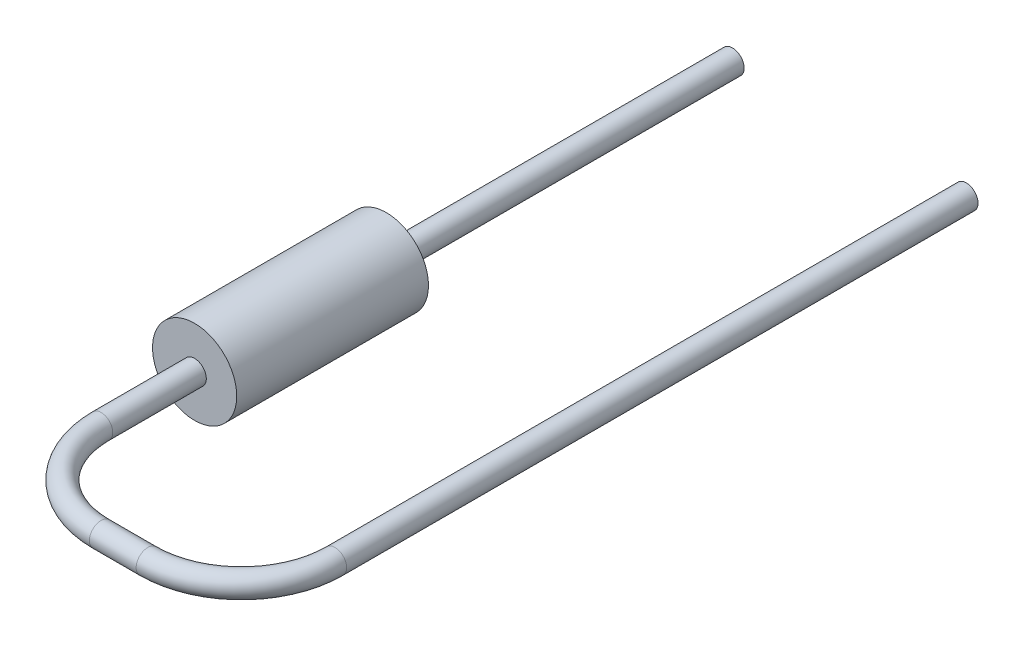
SolidWorks part; units mm, degrees
ref_plane "Top Plane" through (0, 0, 0) normal (0, 0, 1) x (1, 0, 0)
ref_plane "Front Plane" through (0, 0, 0) normal (0, 1, 0) x (1, 0, 0)
ref_plane "Right Plane" through (0, 0, 0) normal (1, 0, 0) x (0, 0, -1)
sketch "Sketch2" plane through (0, 0, 0) normal (0, 0, 1) x (1, 0, 0)
  circle A0 centre (0, 0) radius 0.9
  dimension "D1" = 1.8
extrude "Resistor Body" add sketch "Sketch2" along normal blind 4.1
sketch "Lead1 Path" plane through (0, 0, 0) normal (0, 1, 0) x (1, 0, 0)
  line L0 (5, -6.1) -> (5, 7.4)
  line L1 (-0.9, -4.1) -> (0.9, -4.1) construction
  line L2 (0, -4.1) -> (0, 0) construction
  line L3 (0, -4.1) -> (0, -6.1)
  line L5 (2, -8.1) -> (3, -8.1)
  arc A0 (2, -8.1) -> (0, -6.1) centre (2, -6.1) cw
  arc A1 (5, -6.1) -> (3, -8.1) centre (3, -6.1) cw
  point P9 (0, -8.1)
  point P11 (0, -8.1)
  dimension "D4" = 5
  dimension "D1" = 2
  dimension "D2" = 4
  dimension "D3" = 15.5
sketch "Lead1 Profile" plane through (0, 0, 4.1) normal (0, 0, 1) x (-1, 0, 0)
  circle A0 centre (0, 0) radius 0.25
  dimension "D1" = 0.5
sweep "Lead1" add profiles "Lead1 Profile" path "Lead1 Path"
sketch "Sketch6" plane through (0, 0, 0) normal (0, 0, 1) x (1, 0, 0)
  circle A0 centre (0, 0) radius 0.25 construction
  circle A1 centre (0, 0) radius 0.25
extrude "Lead2" add sketch "Sketch6" along normal up to surface (7.4 mm away)
ref_plane "Mounting Plane" through (0, 0, -4) normal (0, 0, 1) x (1, 0, 0)
sketch "Component_Outline" plane through (0, 0, -4) normal (0, 0, 1) x (1, 0, 0)
  line L0 (0.8646, 0.25) -> (5, 0.25)
  line L1 (2, 0.25) -> (0, 0.25) construction
  line L2 (5, -0.25) -> (0.8646, -0.25)
  line L3 (0, -0.25) -> (2, -0.25) construction
  arc A0 (0.8646, 0.25) -> (0.8646, -0.25) centre (0, 0) ccw
  arc A1 (5, 0.25) -> (5, -0.25) centre (5, 0) cw
  circle A2 centre (5, 0) radius 0.25 construction
  dimension "D1" = 1.8
